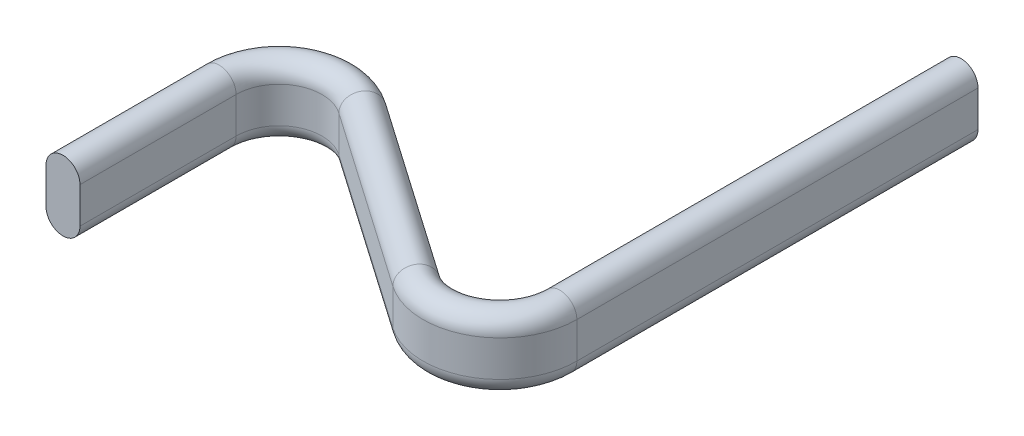
SolidWorks part; units mm, degrees
ref_plane "Front Plane" through (0, 0, 0) normal (0, 0, 1) x (1, 0, 0)
ref_plane "Top Plane" through (0, 0, 0) normal (0, 1, 0) x (1, 0, 0)
ref_plane "Right Plane" through (0, 0, 0) normal (1, 0, 0) x (0, 0, -1)
sketch "Sketch1" plane through (0, 0, 0) normal (0, 0, 1) x (1, 0, 0)
  line L0 (0, -1.8) -> (0, 1.8) construction
  line L1 (-1.7, -1.8) -> (-1.7, 1.8)
  line L2 (1.7, -1.8) -> (1.7, 1.8)
  arc A0 (-1.7, -1.8) -> (1.7, -1.8) centre (0, -1.8) ccw
  arc A1 (1.7, 1.8) -> (-1.7, 1.8) centre (0, 1.8) ccw
  point P2 (0, 0)
  dimension "D2" = 1.7
  dimension "D1" = 3.6
sketch "Sketch2" plane through (0, 0, 0) normal (0, 1, 0) x (1, 0, 0)
  line L0 (0, 0) -> (0, 15.6317)
  line L1 (9.424, 20.5588) -> (27.1431, 8.2452)
  line L2 (36.5671, 13.1723) -> (36.5671, 53.3286)
  arc A0 (0, 15.6317) -> (9.424, 20.5588) centre (6, 15.6317) cw
  arc A1 (27.1431, 8.2452) -> (36.5671, 13.1723) centre (30.5671, 13.1723) ccw
  point P3 (10.5807, 7.6577)
  point P6 (0, 16.394)
  point P7 (16.0419, 8.0816)
  point P8 (19.2235, 23.607)
  point P9 (19.3081, 7.8299)
  point P14 (41.8648, 59.1819)
  point P15 (0, 0)
  point P16 (33.495, 53.3286)
  point P17 (24.7164, 17.017)
  point P19 (0, 9.6897)
  point P20 (26.2411, -34.5983)
  point P21 (0, 14.8655)
  point P22 (0, 0)
  point P23 (24.7164, -40.4013)
  point P24 (0, 0)
  point P25 (27.1431, 8.2452)
  dimension "D1" = 6
sweep "Sweep1" add profiles "Sketch1" path "Sketch2"
